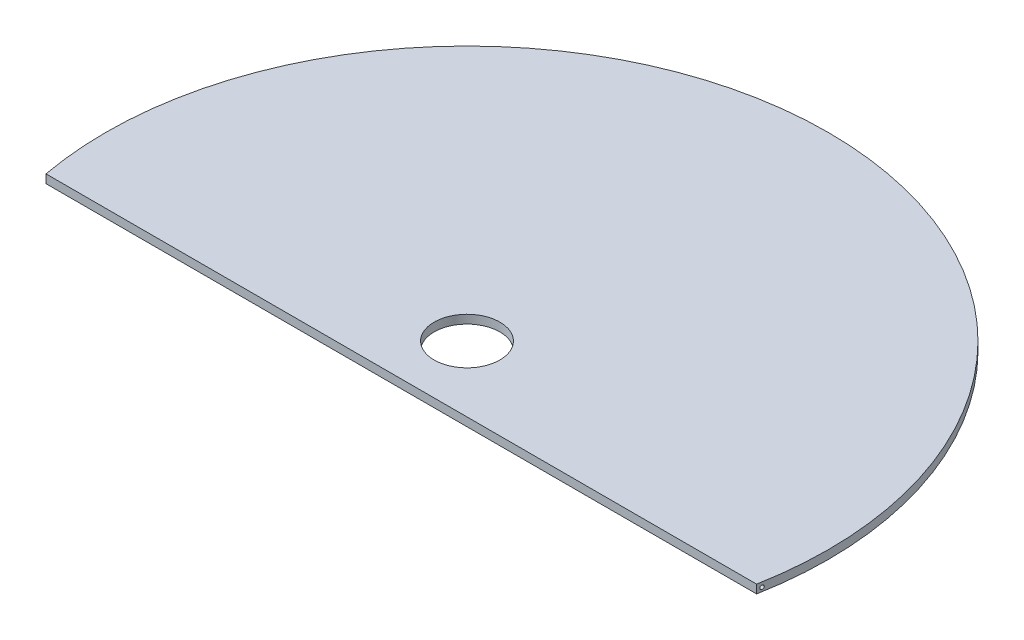
SolidWorks part; units mm, degrees
ref_plane "Front Plane" through (0, 0, 0) normal (0, 0, 1) x (1, 0, 0)
ref_plane "Top Plane" through (0, 0, 0) normal (0, 1, 0) x (1, 0, 0)
ref_plane "Right Plane" through (0, 0, 0) normal (1, 0, 0) x (0, 0, -1)
sketch "Sketch1" plane through (0, 0, 0) normal (0, 1, 0) x (1, 0, 0)
  line L0 (-137.3715, -25.4) -> (137.3715, -25.4)
  circle A0 centre (0, 0) radius 139.7
  circle A1 centre (0, 0) radius 12.7
  dimension "D1" = 279.4
  dimension "D2" = 25.4
  dimension "D3" = 25.4
extrude "Boss-Extrude2" add sketch "Sketch1" along normal blind 3.302 contours L0 A0 A1
sketch "Sketch4" plane through (0, 0, 0) normal (1, 0, 0) x (0, 0, -1)
  line L0 (139.7, 3.302) -> (-25.4, 3.302) construction
  line L1 (-25.4, 3.302) -> (-25.4, 0) construction
  circle A0 centre (-23.622, 1.524) radius 0.7448
  dimension "D1" = 1.778
  dimension "D2" = 1.778
extrude "Cut-Extrude4" cut sketch "Sketch4" against normal through all both and the other way through all
